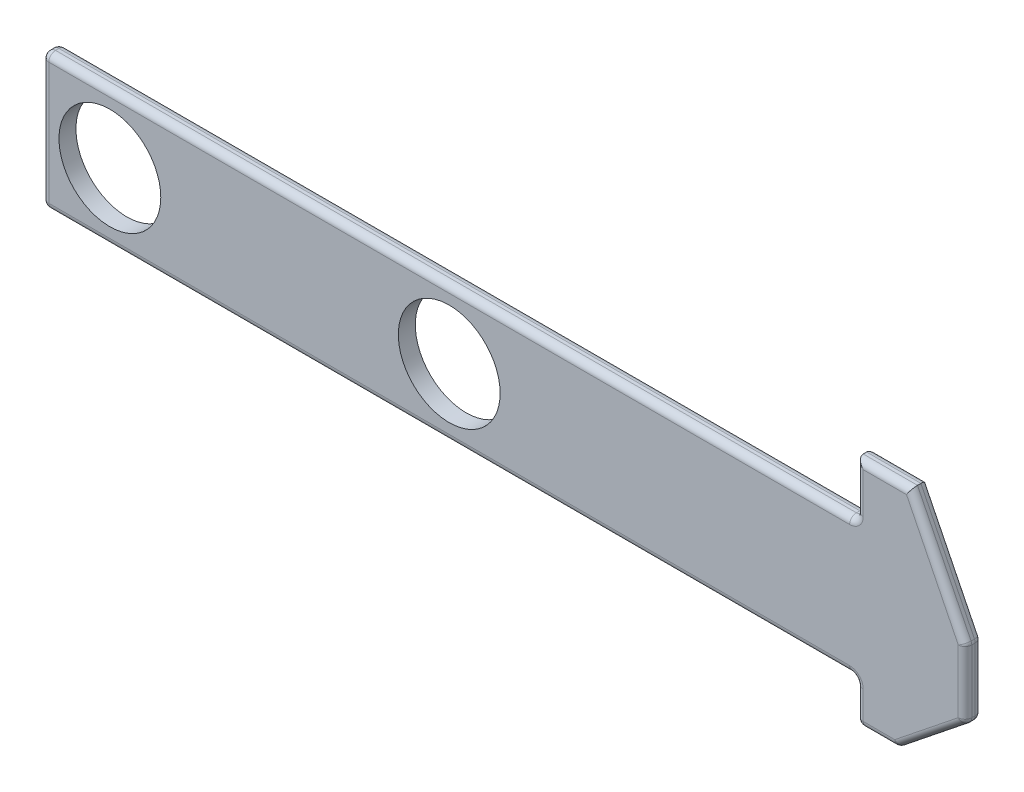
SolidWorks part; units mm, degrees
ref_plane "Front Plane" through (0, 0, 0) normal (0, 0, 1) x (1, 0, 0)
ref_plane "Top Plane" through (0, 0, 0) normal (0, 1, 0) x (1, 0, 0)
ref_plane "Right Plane" through (0, 0, 0) normal (1, 0, 0) x (0, 0, -1)
sketch "Sketch1" plane through (0, 0, 0) normal (0, 0, 1) x (1, 0, 0)
  line L0 (-76.2, 12.7) -> (76.2, 12.7)
  line L1 (-139.7, 107.95) -> (139.7, 107.95) construction
  line L2 (-139.7, 107.95) -> (-139.7, -107.95) construction
  line L3 (-139.7, -107.95) -> (139.7, -107.95) construction
  line L4 (139.7, 107.95) -> (139.7, -107.95) construction
  line L5 (-139.7, 107.95) -> (139.7, -107.95) construction
  line L6 (-139.7, -107.95) -> (139.7, 107.95) construction
  line L7 (0, 12.7) -> (0, -12.7) construction
  line L18 (76.2, 12.7) -> (76.2, 22.86)
  line L19 (76.2, 22.86) -> (86.36, 22.86)
  line L20 (86.36, 22.86) -> (96.52, 2.3819)
  line L21 (96.52, 2.3819) -> (96.52, -10.3181)
  line L22 (96.52, -10.3181) -> (83.82, -20.4781)
  line L23 (83.82, -20.4781) -> (76.2, -20.4781)
  line L24 (76.2, -20.4781) -> (76.2, -12.7)
  line L25 (76.2, -12.7) -> (-76.2, -12.7)
  line L26 (-76.2, -12.7) -> (-76.2, 12.7)
  point P8 (0, 12.7)
  point P17 (0, 0)
  point P19 (0, 12.7)
  dimension "D1" = 279.4
  dimension "D2" = 215.9
  dimension "D3" = 152.4
  dimension "D4" = 25.4
  dimension "D5" = 10.16
  dimension "D6" = 22.86
  dimension "D7" = 12.7
  dimension "D8" = 10.16
  dimension "D9" = 7.62
  dimension "D10" = 172.72
  dimension "D11" = 10.16
extrude "Boss-Extrude1" add sketch "Sketch1" along normal blind 3.175
sketch "Sketch2" plane through (0, 0, 3.175) normal (0, 0, 1) x (1, 0, 0)
  line L0 (-76.2, 0) -> (-63.5, 0) construction
  line L4 (-76.2, 12.7) -> (-76.2, -12.7) construction
  circle A0 centre (-63.5, 0) radius 9.525
  circle A1 centre (0, 0) radius 9.525
  dimension "D2" = 19.05
  dimension "D3" = 19.05
  dimension "D1" = 12.7
extrude "Cut-Extrude1" cut sketch "Sketch2" against normal through all
fillet "Fillet1" radius 1.27 28 edges at (76.2, -12.7, 1.5875) (76.2, -16.5891, 3.175) (80.01, -20.4781, 3.175) (76.2, -20.4781, 1.5875) (83.82, -20.4781, 1.5875) (96.52, -10.3181, 1.5875) (96.52, 2.3819, 1.5875) (90.17, -15.3981, 3.175) (96.52, -3.9681, 3.175) (91.44, 12.6209, 3.175) (81.28, 22.86, 3.175) (76.2, 17.78, 3.175) (76.2, 12.7, 1.5875) (76.2, 17.78, 0) (81.28, 22.86, 0) (91.44, 12.6209, 0) (96.52, -3.9681, 0) (90.17, -15.3981, 0) (80.01, -20.4781, 0) (76.2, -16.5891, 0) (0, -12.7, 0) (0, -12.7, 3.175) (-76.2, -12.7, 1.5875) (-76.2, 0, 0) (-76.2, 0, 3.175) (-76.2, 12.7, 1.5875) (0, 12.7, 0) (0, 12.7, 3.175)
